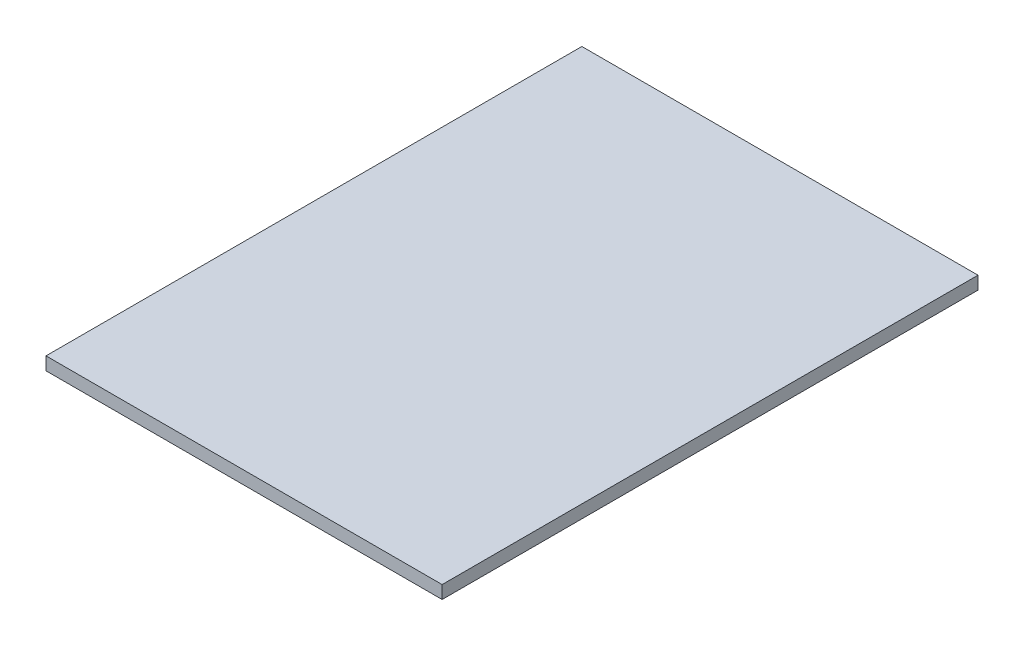
SolidWorks part; units mm, degrees
ref_plane "Спереди" through (0, 0, 0) normal (0, 0, 1) x (1, 0, 0)
ref_plane "Сверху" through (0, 0, 0) normal (0, 1, 0) x (1, 0, 0)
ref_plane "Справа" through (0, 0, 0) normal (1, 0, 0) x (0, 0, -1)
sketch "Эскиз1" plane through (0, 0, 0) normal (0, 1, 0) x (1, 0, 0)
  line L1 (275, -372) -> (-275, -372)
  line L2 (275, -372) -> (275, 372)
  line L3 (275, 372) -> (-275, 372)
  line L4 (-275, -372) -> (-275, 372)
  line L5 (275, -372) -> (-275, 372) construction
  line L6 (275, 372) -> (-275, -372) construction
  point P0 (0, 0)
  dimension "D1" = 550
  dimension "D2" = 744
extrude "Бобышка-Вытянуть1" add sketch "Эскиз1" along normal blind 18
